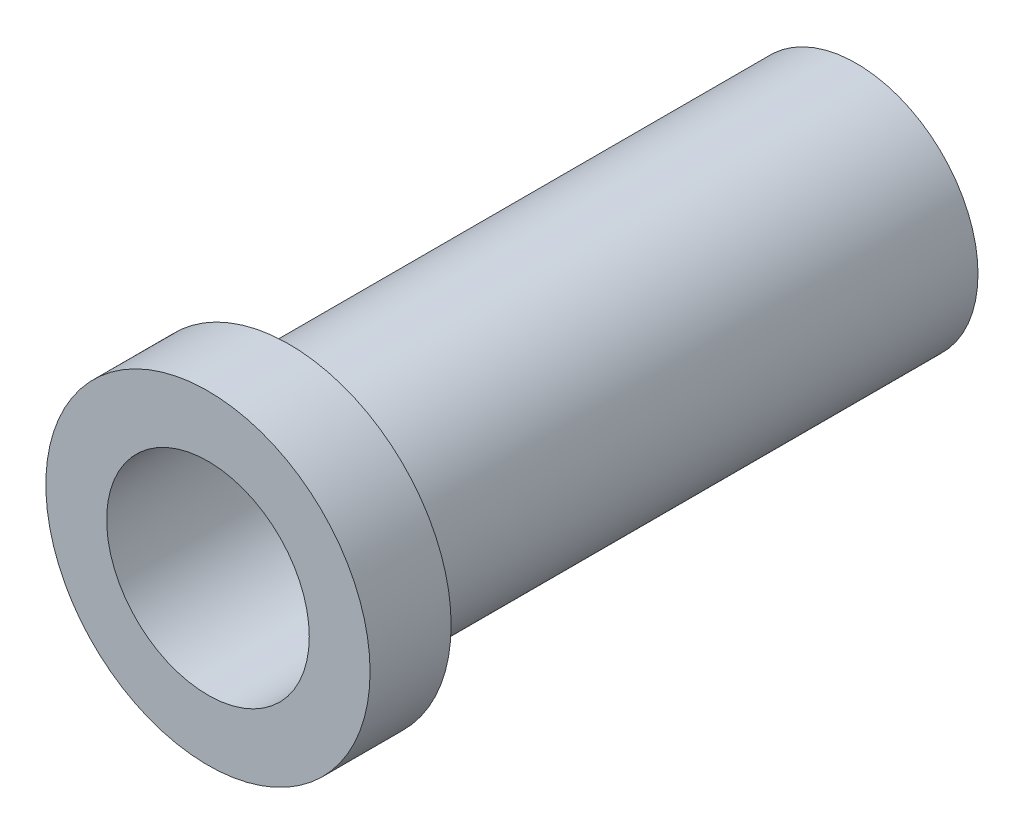
SolidWorks part; units mm, degrees
material "Nylon 101"
ref_plane "Front Plane" through (0, 0, 0) normal (0, 0, 1) x (1, 0, 0)
ref_plane "Top Plane" through (0, 0, 0) normal (0, 1, 0) x (1, 0, 0)
ref_plane "Right Plane" through (0, 0, 0) normal (1, 0, 0) x (0, 0, -1)
sketch "Sketch1" plane through (0, 0, 0) normal (0, 0, 1) x (1, 0, 0)
  circle A0 centre (0, 0) radius 19.05
  dimension "D1" = 38.1
extrude "Boss-Extrude1" add sketch "Sketch1" along normal blind 101.6
sketch "Sketch2" plane through (0, 0, 101.6) normal (0, 0, 1) x (1, 0, 0)
  circle A0 centre (0, 0) radius 15.875
  dimension "D1" = 31.75
extrude "Cut-Extrude1" cut sketch "Sketch2" against normal blind 101.6
sketch "Sketch3" plane through (0, 0, 101.6) normal (0, 0, 1) x (1, 0, 0)
  circle A0 centre (0, 0) radius 25.4
  dimension "D1" = 50.8
extrude "Boss-Extrude2" add sketch "Sketch3" against normal blind 12.7
sketch "Sketch4" plane through (0, 0, 101.6) normal (0, 0, 1) x (1, 0, 0)
  circle A0 centre (0, 0) radius 15.875
  dimension "D1" = 31.75
extrude "Cut-Extrude2" cut sketch "Sketch4" against normal blind 12.7
